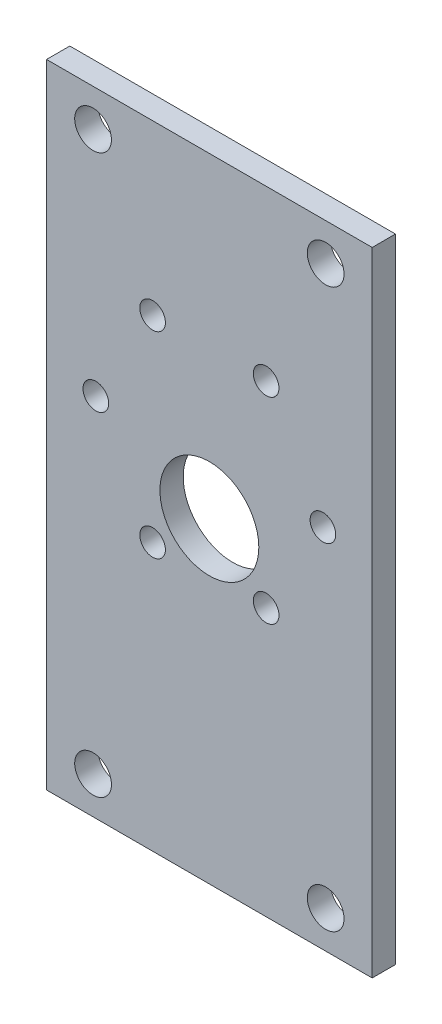
SolidWorks part; units mm, degrees
ref_plane "Спереди" through (0, 0, 0) normal (0, 0, 1) x (1, 0, 0)
ref_plane "Сверху" through (0, 0, 0) normal (0, 1, 0) x (1, 0, 0)
ref_plane "Справа" through (0, 0, 0) normal (1, 0, 0) x (0, 0, -1)
sketch "Эскиз1" plane through (0, 0, 0) normal (0, 0, 1) x (1, 0, 0)
  line L0 (0, 86.36) -> (0, 0) construction
  line L1 (22.225, 86.36) -> (-22.225, 86.36)
  line L2 (22.225, 86.36) -> (22.225, 35.56)
  line L4 (-22.225, 86.36) -> (-22.225, 35.56)
  line L5 (-15.5, 49.93) -> (-7.75, 36.5066) construction
  line L6 (-7.75, 36.5066) -> (7.75, 36.5066) construction
  line L7 (7.75, 36.5066) -> (15.5, 49.93) construction
  line L8 (15.5, 49.93) -> (7.75, 63.3534) construction
  line L9 (7.75, 63.3534) -> (-7.75, 63.3534) construction
  line L10 (-7.75, 63.3534) -> (-15.5, 49.93) construction
  line L12 (22.225, 35.56) -> (22.225, 0)
  line L13 (22.225, 0) -> (-22.225, 0)
  line L14 (-22.225, 35.56) -> (-22.225, 0)
  circle A0 centre (0, 49.93) radius 13.4234 construction
  circle A1 centre (-7.75, 63.3534) radius 1.75
  circle A2 centre (-15.5, 49.93) radius 1.75
  circle A3 centre (-7.75, 36.5066) radius 1.75
  circle A4 centre (7.75, 36.5066) radius 1.75
  circle A5 centre (15.5, 49.93) radius 1.75
  circle A6 centre (7.75, 63.3534) radius 1.75
  circle A7 centre (0, 43.18) radius 6.75
  circle A8 centre (15.875, 81.28) radius 2.5083
  circle A9 centre (-15.875, 81.28) radius 2.5083
  circle A10 centre (15.875, 5.08) radius 2.5083
  circle A11 centre (-15.875, 5.08) radius 2.5083
  point P30 (0, 43.18)
  point P31 (0, 0)
  point P32 (0, 0)
  dimension "D6" = 3.5
  dimension "D8" = 13.5
  dimension "D9" = 5.0165
  dimension "D17" = 5.0165
  dimension "D1" = 50.8
  dimension "D2" = 44.45
  dimension "D3" = 7.75
  dimension "D4" = 22.225
  dimension "D5" = 31
  dimension "D10" = 31.75
  dimension "D11" = 6.35
  dimension "D12" = 35.56
  dimension "D13" = 6.35
  dimension "D14" = 31.75
  dimension "D15" = 5.08
  dimension "D16" = 5.08
  dimension "D20" = 15.875
extrude "Бобышка-Вытянуть1" add sketch "Эскиз1" along normal blind 3.175
